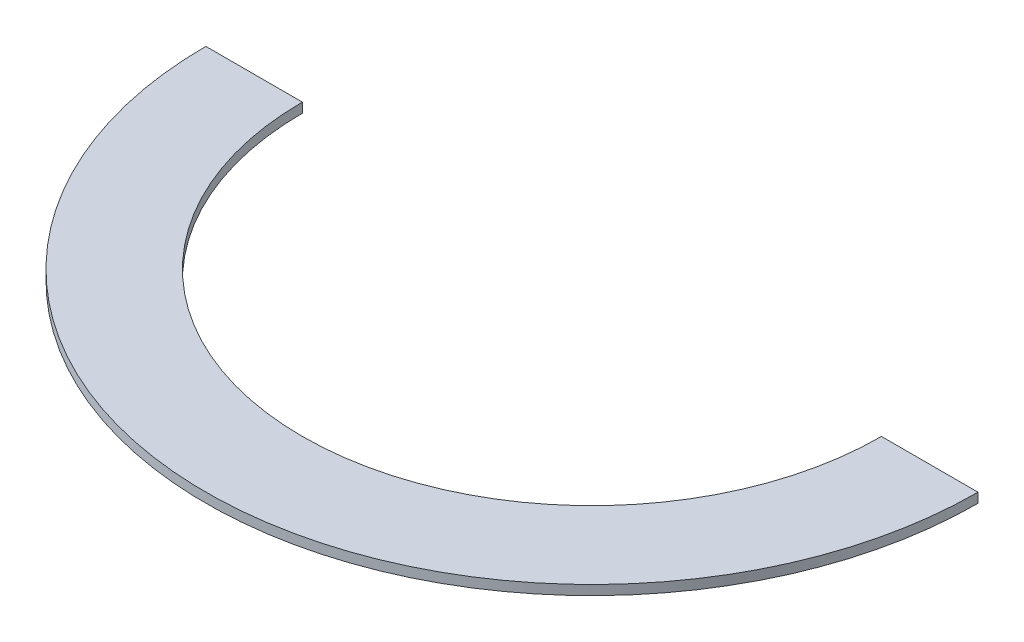
SolidWorks part; units mm, degrees
ref_plane "Face" through (0, 0, 0) normal (0, 0, 1) x (1, 0, 0)
ref_plane "Dessus" through (0, 0, 0) normal (0, 1, 0) x (1, 0, 0)
ref_plane "Droite" through (0, 0, 0) normal (1, 0, 0) x (0, 0, -1)
sketch "Esquisse1" plane through (0, 0, 0) normal (0, 1, 0) x (1, 0, 0)
  line L0 (0, 0) -> (100, 0)
  line L1 (0, 0) -> (800, 0) construction
  line L2 (400, 0) -> (400, -400) construction
  line L3 (700, 0) -> (800, 0)
  arc A0 (0, 0) -> (800, 0) centre (400, 0) ccw
  arc A1 (100, 0) -> (700, 0) centre (400, 0) ccw
  dimension "D1" = 400
  dimension "D2" = 300
extrude "Extrusion1" add sketch "Esquisse1" along normal blind 10
